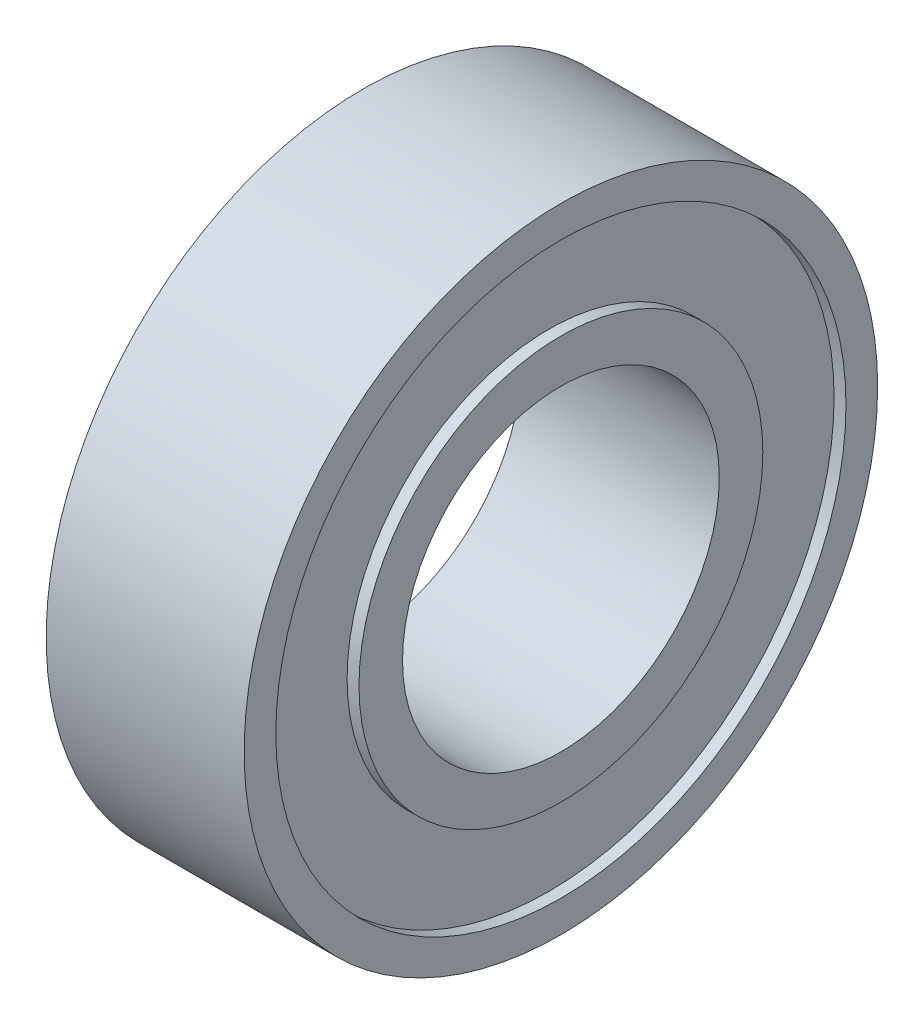
SolidWorks part; units mm, degrees
material "Plain Carbon Steel"
ref_plane "Front Plane" through (0, 0, 0) normal (0, 0, 1) x (1, 0, 0)
ref_plane "Top Plane" through (0, 0, 0) normal (0, 1, 0) x (1, 0, 0)
ref_plane "Right Plane" through (0, 0, 0) normal (1, 0, 0) x (0, 0, -1)
sketch "Sketch1" plane through (0, 0, 0) normal (0, 0, 1) x (1, 0, 0)
  line L0 (2.5, 4) -> (-2.5, 4)
  line L1 (-2.5, 4) -> (-2.5, 5.1)
  line L2 (-2.5, 5.1) -> (-2.2, 5.1)
  line L3 (-2.2, 5.1) -> (-2.2, 7.2)
  line L4 (-2.2, 7.2) -> (-2.5, 7.2)
  line L5 (-2.5, 7.2) -> (-2.5, 8)
  line L6 (-2.5, 8) -> (2.5, 8)
  line L7 (0, 8) -> (0, 4) construction
  line L8 (2.5, 7.2) -> (2.5, 8)
  line L9 (2.2, 7.2) -> (2.5, 7.2)
  line L10 (2.2, 5.1) -> (2.2, 7.2)
  line L11 (2.5, 5.1) -> (2.2, 5.1)
  line L12 (2.5, 4) -> (2.5, 5.1)
  line L13 (0, 0) -> (-4.3663, 0) construction
  dimension "D1" = 8
  dimension "D2" = 16
  dimension "D3" = 5
  dimension "D4" = 10.2
  dimension "D5" = 2.1
  dimension "D6" = 0.3
revolve "Revolve1" add sketch "Sketch1" angle 360 about L13
